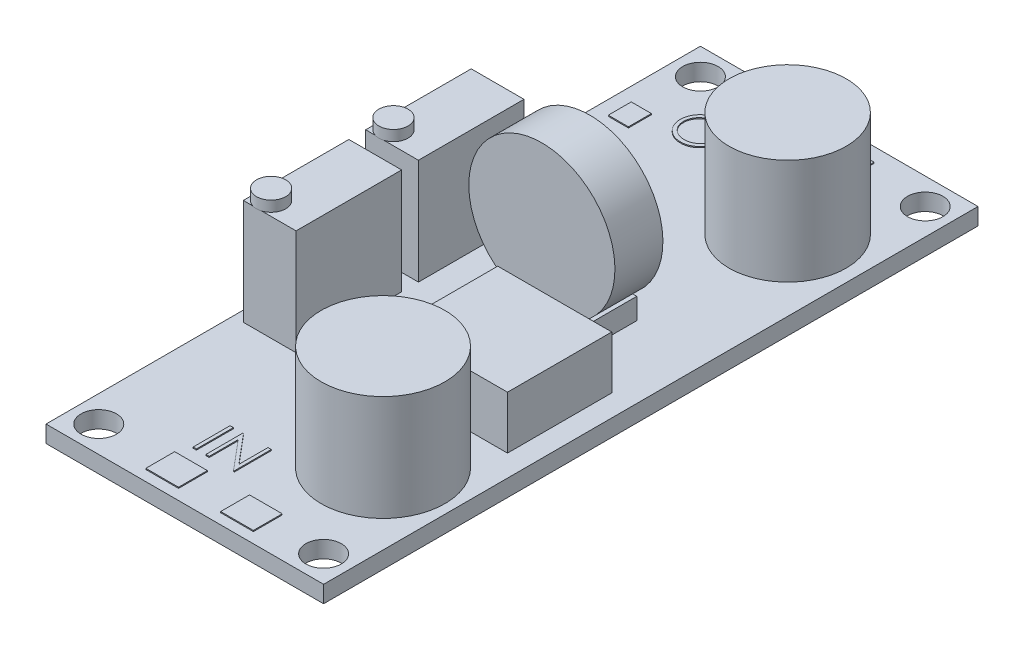
SolidWorks part; units mm, degrees
ref_plane "Front Plane" through (0, 0, 0) normal (0, 0, 1) x (1, 0, 0)
ref_plane "Top Plane" through (0, 0, 0) normal (0, 1, 0) x (1, 0, 0)
ref_plane "Right Plane" through (0, 0, 0) normal (1, 0, 0) x (0, 0, -1)
sketch "Sketch1" plane through (0, 0, 0) normal (0, 1, 0) x (1, 0, 0)
  line L0 (-60.8029, -3.4678) -> (63.7852, -3.4678)
  line L1 (-17.8407, 27.5322) -> (8.4593, 27.5322)
  line L2 (-17.8407, 27.5322) -> (-17.8407, -34.4678)
  line L3 (-17.8407, -34.4678) -> (8.4593, -34.4678)
  line L4 (8.4593, 27.5322) -> (8.4593, -34.4678)
  circle A0 centre (5.9593, 25.0322) radius 1.675
  circle A1 centre (-15.3407, 25.0322) radius 1.675
  circle A2 centre (-15.3407, -31.9678) radius 1.675
  circle A3 centre (5.9593, -31.9678) radius 1.675
  dimension "D3" = 3.35
  dimension "D4" = 2.5
  dimension "D5" = 2.5
  dimension "D6" = 3.35
  dimension "D8" = 2.5
  dimension "D1" = 62
  dimension "D2" = 26.3
  dimension "D7" = 2.5
  dimension "D9" = 31
extrude "Boss-Extrude1" add sketch "Sketch1" along normal blind 1.6 contours L4 L0 L2 L3 A2 A3 | L4 L1 L2 L0 A1 A0
sketch "Sketch2" plane through (0, 1.6, 0) normal (0, 1, 0) x (1, 0, 0)
  line L1 (-16.8428, 4.8197) -> (-11.8428, 4.8197)
  line L2 (-16.8428, 4.8197) -> (-16.8428, -5.1803)
  line L3 (-16.8428, -5.1803) -> (-11.8428, -5.1803)
  line L4 (-11.8428, 4.8197) -> (-11.8428, -5.1803)
  line L5 (-16.8428, -6.7726) -> (-11.8428, -6.7726)
  line L6 (-16.8428, -6.7726) -> (-16.8428, -16.7726)
  line L7 (-16.8428, -16.7726) -> (-11.8428, -16.7726)
  line L8 (-11.8428, -6.7726) -> (-11.8428, -16.7726)
  dimension "D1" = 10
  dimension "D2" = 10
  dimension "D3" = 5
  dimension "D4" = 5
extrude "Boss-Extrude2" add sketch "Sketch2" along normal blind 10
sketch "Sketch3" plane through (0, 11.6, 0) normal (0, 1, 0) x (1, 0, 0)
  circle A0 centre (-15.5255, -15.4553) radius 1.3832
  circle A1 centre (-15.5255, -3.863) radius 1.3832
extrude "Boss-Extrude3" add sketch "Sketch3" along normal blind 1
sketch "Sketch4" plane through (0, 1.6, 0) normal (0, 1, 0) x (1, 0, 0)
  circle A0 centre (1.7312, 16.226) radius 5.5472
  circle A1 centre (1.7312, -22.1077) radius 5.862
extrude "Boss-Extrude4" add sketch "Sketch4" along normal blind 10
sketch "Sketch5" plane through (0, 1.6, 0) normal (0, 1, 0) x (1, 0, 0)
  line L1 (-5.7775, 1.999) -> (1.6653, 1.999)
  line L2 (-5.7775, 1.999) -> (-5.7775, -2.5457)
  line L3 (-5.7775, -2.5457) -> (1.6653, -2.5457)
  line L4 (1.6653, 1.999) -> (1.6653, -2.5457)
extrude "Boss-Extrude5" add sketch "Sketch5" along normal blind 2
sketch "Sketch6" plane through (0, 0, 2.5457) normal (0, 0, 1) x (1, 0, 0)
  line L0 (-19.534, 16) -> (11.7234, 16)
  line L1 (-17.8407, 0) -> (8.4593, 0) construction
  circle A0 centre (-2.7823, 9.3223) radius 6.9228
  dimension "D1" = 16
extrude "Boss-Extrude6" add sketch "Sketch6" against normal up to vertex contours A0
sketch "Sketch7" plane through (0, 1.6, 0) normal (0, 1, 0) x (1, 0, 0)
  line L1 (-4.3943, -5.1144) -> (6.4076, -5.1144)
  line L2 (-4.3943, -5.1144) -> (-4.3943, -14.9942)
  line L3 (-4.3943, -14.9942) -> (6.4076, -14.9942)
  line L4 (6.4076, -5.1144) -> (6.4076, -14.9942)
extrude "Boss-Extrude7" add sketch "Sketch7" along normal blind 5
sketch "Sketch8" plane through (0, 1.6, 0) normal (0, 1, 0) x (1, 0, 0)
  line L1 (-10.4608, 26.1447) -> (-7.4, 26.1447)
  line L2 (-10.4608, 26.1447) -> (-10.4608, 23.3989)
  line L3 (-10.4608, 23.3989) -> (-7.4, 23.3989)
  line L4 (-7.4, 26.1447) -> (-7.4, 23.3989)
  line L5 (-2.6737, 26.1447) -> (0, 26.1447)
  line L6 (-2.6737, 26.1447) -> (-2.6737, 23.3989)
  line L7 (-2.6737, 23.3989) -> (0, 23.3989)
  line L8 (0, 26.1447) -> (0, 23.3989)
  line L9 (-9.3774, -30.7411) -> (-6.2787, -30.7411)
  line L10 (-9.3774, -30.7411) -> (-9.3774, -33.4721)
  line L11 (-9.3774, -33.4721) -> (-6.2787, -33.4721)
  line L12 (-6.2787, -30.7411) -> (-6.2787, -33.4721)
  line L13 (-2.2872, -30.7411) -> (0.8115, -30.7411)
  line L14 (-2.2872, -30.7411) -> (-2.2872, -33.4721)
  line L15 (-2.2872, -33.4721) -> (0.8115, -33.4721)
  line L16 (0.8115, -30.7411) -> (0.8115, -33.4721)
extrude "Boss-Extrude8" add sketch "Sketch8" along normal blind 0.1
sketch "Sketch9" plane through (0, 1.6, 0) normal (0, 1, 0) x (1, 0, 0)
  text T0 "OUT"
  point P1 (-12.9568, 18.7289)
extrude "Boss-Extrude9" add sketch "Sketch9" along normal blind 0.1
sketch "Sketch10" plane through (0, 1.6, 0) normal (0, 1, 0) x (1, 0, 0)
  text T0 "IN"
  point P1 (-11.3102, -29.5505)
  point P2 (-9.3342, -29.4846)
extrude "Boss-Extrude10" add sketch "Sketch10" along normal blind 0.1
sketch "Sketch11" plane through (0, 1.6, 0) normal (0, 1, 0) x (1, 0, 0)
  line L1 (-16.4477, 19.5851) -> (-14.5376, 19.5851)
  line L2 (-16.4477, 19.5851) -> (-16.4477, 17.4115)
  line L3 (-16.4477, 17.4115) -> (-14.5376, 17.4115)
  line L4 (-14.5376, 19.5851) -> (-14.5376, 17.4115)
  line L5 (-16.4477, 14.6452) -> (-14.5376, 14.6452)
  line L6 (-16.4477, 14.6452) -> (-16.4477, 11.813)
  line L7 (-16.4477, 11.813) -> (-14.5376, 11.813)
  line L8 (-14.5376, 14.6452) -> (-14.5376, 11.813)
  line L9 (-16.4477, 8.5856) -> (-14.5376, 8.5856)
  line L10 (-16.4477, 8.5856) -> (-16.4477, 6.6096)
  line L11 (-16.4477, 6.6096) -> (-14.5376, 6.6096)
  line L12 (-14.5376, 8.5856) -> (-14.5376, 6.6096)
extrude "Boss-Extrude11" add sketch "Sketch11" along normal blind 0.1
